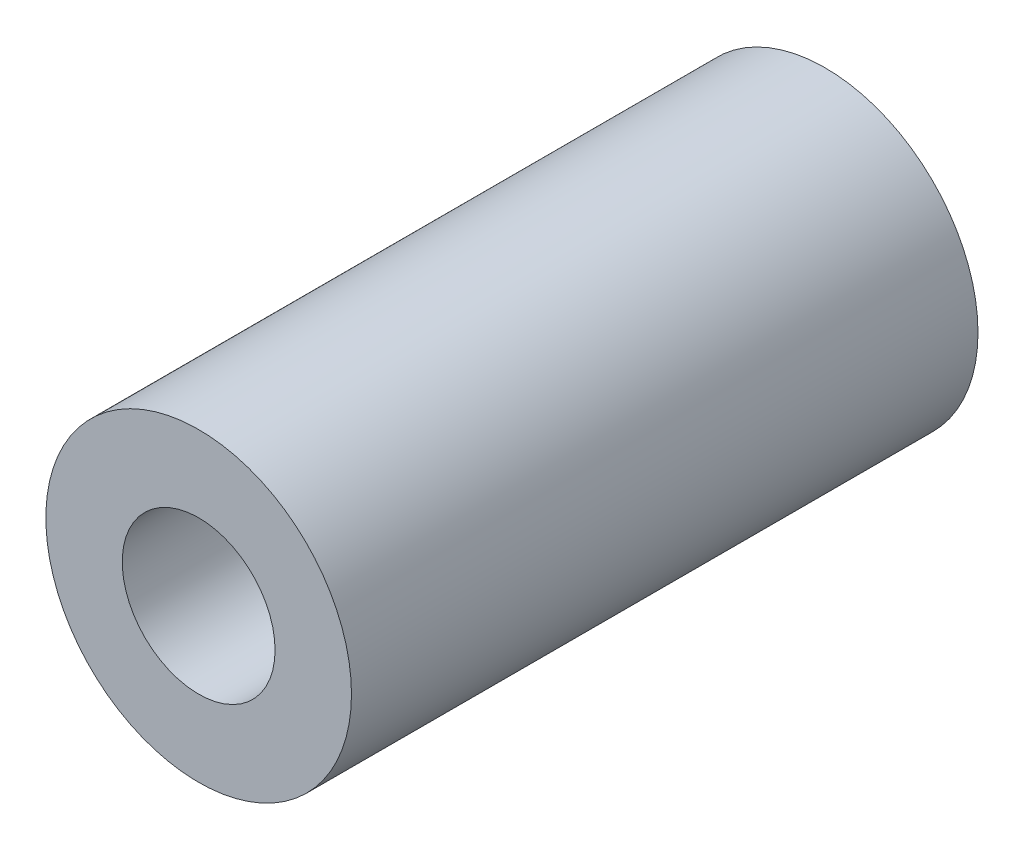
SolidWorks part; units mm, degrees
ref_plane "前视基准面" through (0, 0, 0) normal (0, 0, 1) x (1, 0, 0)
ref_plane "上视基准面" through (0, 0, 0) normal (0, 1, 0) x (1, 0, 0)
ref_plane "右视基准面" through (0, 0, 0) normal (1, 0, 0) x (0, 0, -1)
sketch "草图1" plane through (0, 0, 0) normal (0, 0, 1) x (1, 0, 0)
  circle A0 centre (0, 0) radius 10
  circle A1 centre (0, 0) radius 5
  dimension "D1" = 10
  dimension "D2" = 20
extrude "凸台-拉伸1" add sketch "草图1" along normal blind 41
